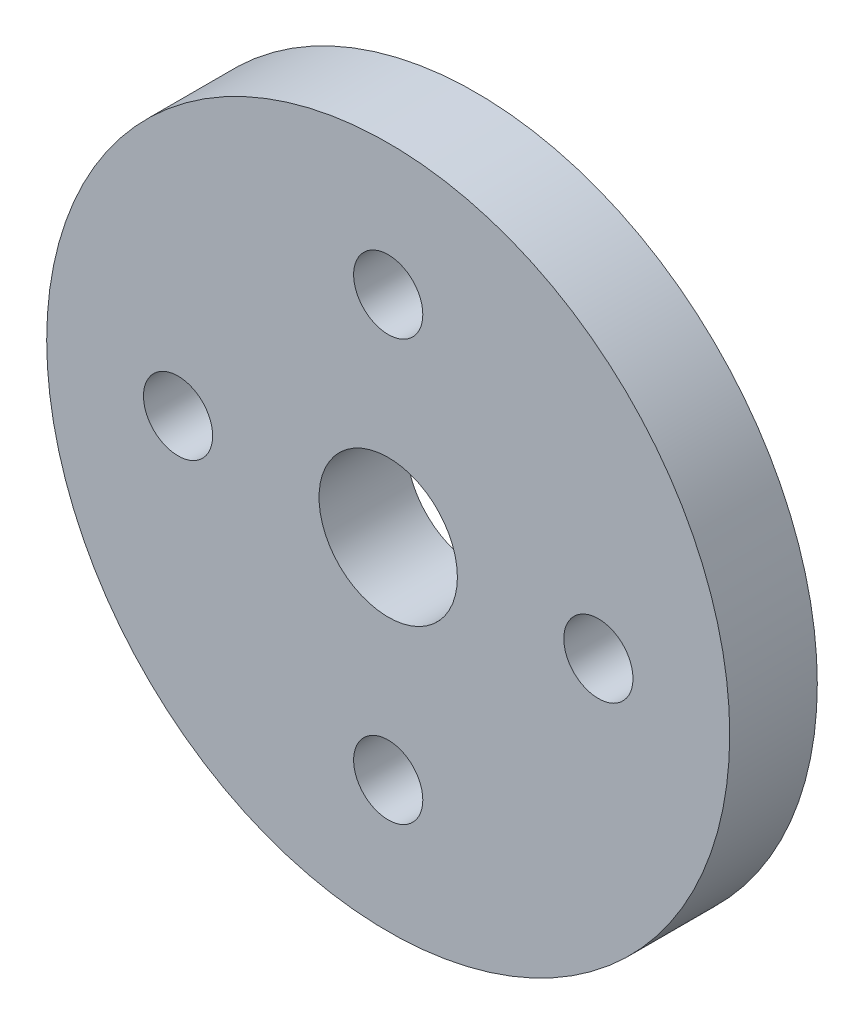
SolidWorks part; units mm, degrees
ref_plane "Front Plane" through (0, 0, 0) normal (0, 0, 1) x (1, 0, 0)
ref_plane "Top Plane" through (0, 0, 0) normal (0, 1, 0) x (1, 0, 0)
ref_plane "Right Plane" through (0, 0, 0) normal (1, 0, 0) x (0, 0, -1)
sketch "Sketch1" plane through (0, 0, 0) normal (0, 0, 1) x (1, 0, 0)
  line L0 (0, 12) -> (0, 0) construction
  circle A0 centre (0, 0) radius 19.5
  circle A1 centre (0, 0) radius 3.95
  circle A2 centre (0, 12) radius 1.975
  circle A3 centre (12, 0) radius 1.975
  circle A4 centre (0, -12) radius 1.975
  circle A5 centre (-12, 0) radius 1.975
  point P15 (0, 0)
  dimension "D1" = 39
  dimension "D2" = 7.9
  dimension "D3" = 3.95
  dimension "D4" = 12
  dimension "D5" = 4
extrude "Boss-Extrude1" add sketch "Sketch1" along normal blind 5
